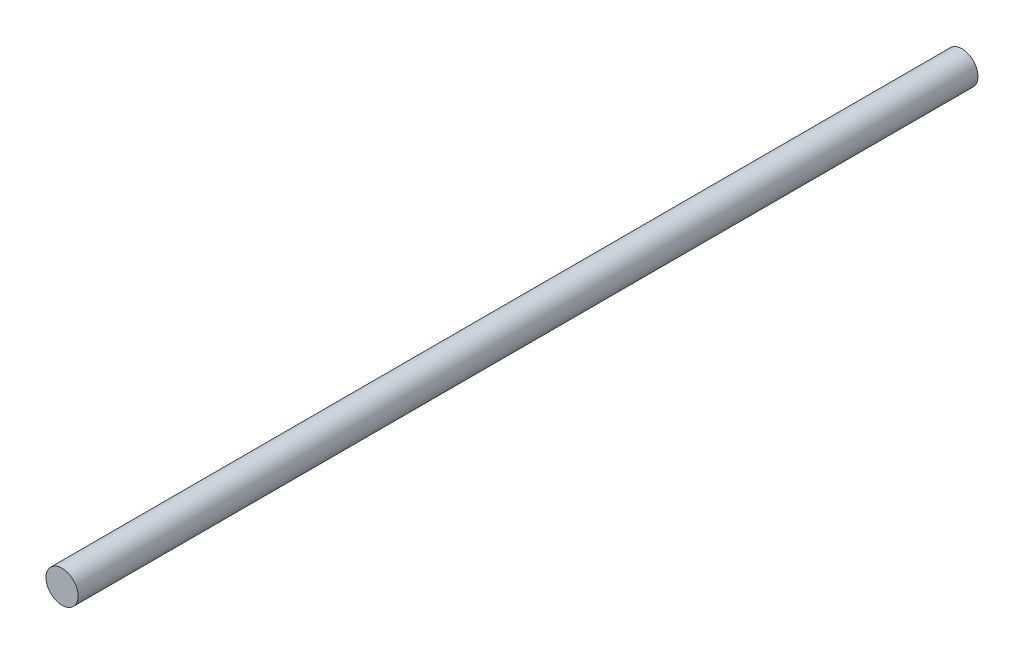
SolidWorks part; units mm, degrees
ref_plane "Front Plane" through (0, 0, 0) normal (0, 0, 1) x (1, 0, 0)
ref_plane "Top Plane" through (0, 0, 0) normal (0, 1, 0) x (1, 0, 0)
ref_plane "Right Plane" through (0, 0, 0) normal (1, 0, 0) x (0, 0, -1)
sketch "Sketch1" plane through (0, 0, 0) normal (0, 0, 1) x (1, 0, 0)
  circle A0 centre (0, 0) radius 5
extrude "Boss-Extrude1" add sketch "Sketch1" along normal blind 280
